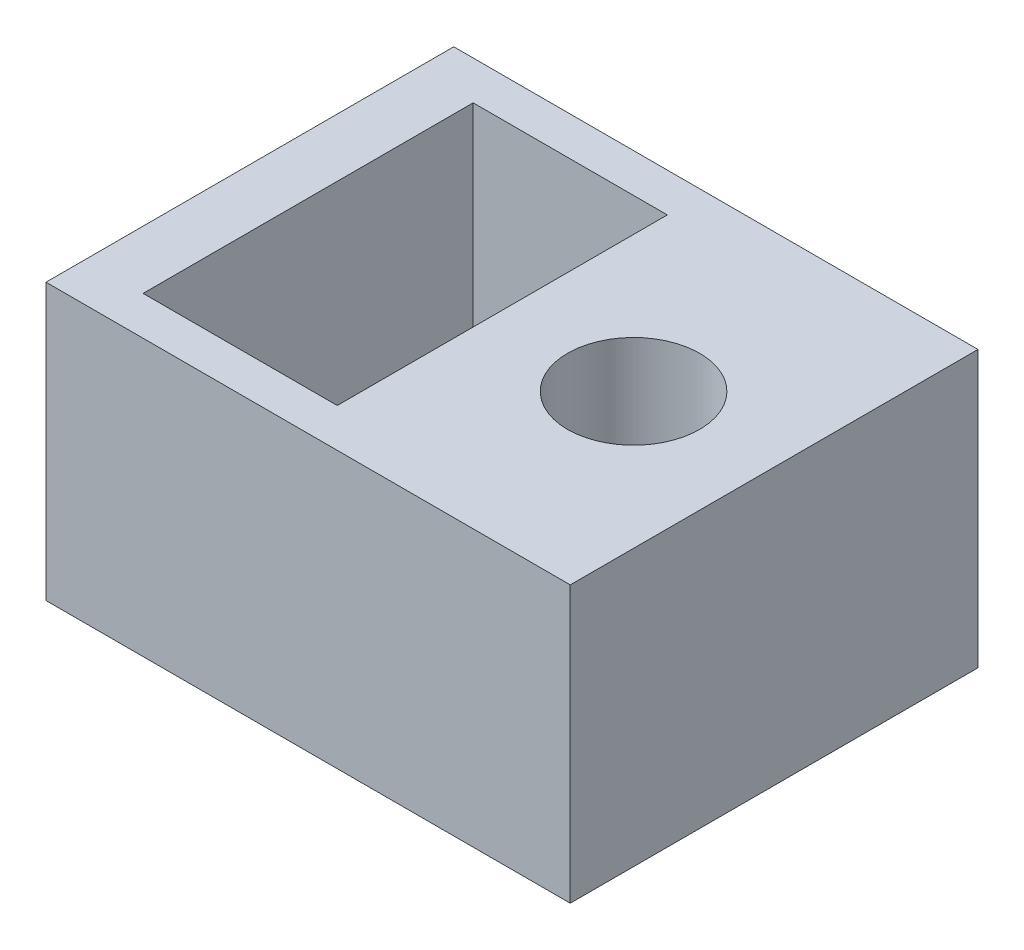
SolidWorks part; units mm, degrees
ref_plane "Alzado" through (0, 0, 0) normal (0, 0, 1) x (1, 0, 0)
ref_plane "Planta" through (0, 0, 0) normal (0, 1, 0) x (1, 0, 0)
ref_plane "Vista lateral" through (0, 0, 0) normal (1, 0, 0) x (0, 0, -1)
sketch "Croquis1" plane through (0, 0, 0) normal (0, 1, 0) x (1, 0, 0)
  line L0 (12.1053, 1.4557) -> (12.1053, -1.9132) construction
  line L1 (8.1053, -7.0443) -> (21.6053, -7.0443)
  line L2 (8.1053, -7.0443) -> (8.1053, 3.4557)
  line L3 (8.1053, 3.4557) -> (21.6053, 3.4557)
  line L4 (21.6053, -7.0443) -> (21.6053, 3.4557)
  line L14 (-1.8947, -1.9132) -> (18.1053, -1.9132) construction
  line L21 (10.6053, 1.4557) -> (10.6053, -5.0443)
  line L22 (10.6053, -5.0443) -> (13.6053, -5.0443)
  line L23 (13.6053, 1.4557) -> (13.6053, -5.0443)
  line L24 (10.6053, 1.4557) -> (13.6053, 1.4557)
  line L25 (12.1053, -1.9132) -> (18.1053, -1.9132) construction
  circle A15 centre (18.1053, -1.9132) radius 1.7
  dimension "D6" = 2
  dimension "D21" = 3.4
  dimension "D3" = 2.5
  dimension "D4" = 3.5
  dimension "D5" = 2
  dimension "D7" = 6
  dimension "D19" = 3
  dimension "D20" = 6.5
  dimension "D22" = 20
extrude "Saliente-Extruir1" add sketch "Croquis1" along normal blind 7.1
sketch "Croquis2" plane through (0, 7.1, 0) normal (0, 1, 0) x (1, 0, 0)
  line L0 (13.6053, 1.4557) -> (10.6053, 1.4557) construction
  line L1 (10.6053, 1.4557) -> (10.6053, -5.0443) construction
  line L2 (10.6053, -5.0443) -> (13.6053, -5.0443) construction
  line L3 (13.6053, -5.0443) -> (13.6053, 1.4557) construction
  line L4 (13.6053, 1.4557) -> (10.6053, 1.4557) construction
  line L5 (10.6053, 1.4557) -> (10.6053, -5.0443) construction
  line L6 (10.6053, -5.0443) -> (13.6053, -5.0443) construction
  line L7 (13.6053, -5.0443) -> (13.6053, 1.4557) construction
  line L8 (14.6053, 2.4557) -> (9.6053, 2.4557)
  line L9 (9.6053, 2.4557) -> (9.6053, -6.0443)
  line L10 (9.6053, -6.0443) -> (14.6053, -6.0443)
  line L11 (14.6053, -6.0443) -> (14.6053, 2.4557)
  dimension "D1" = 1
extrude "Cortar-Extruir1" cut sketch "Croquis2" against normal offset from surface (5.1 mm away) 2 up to face at (14.8553, 0, 1.7943)
